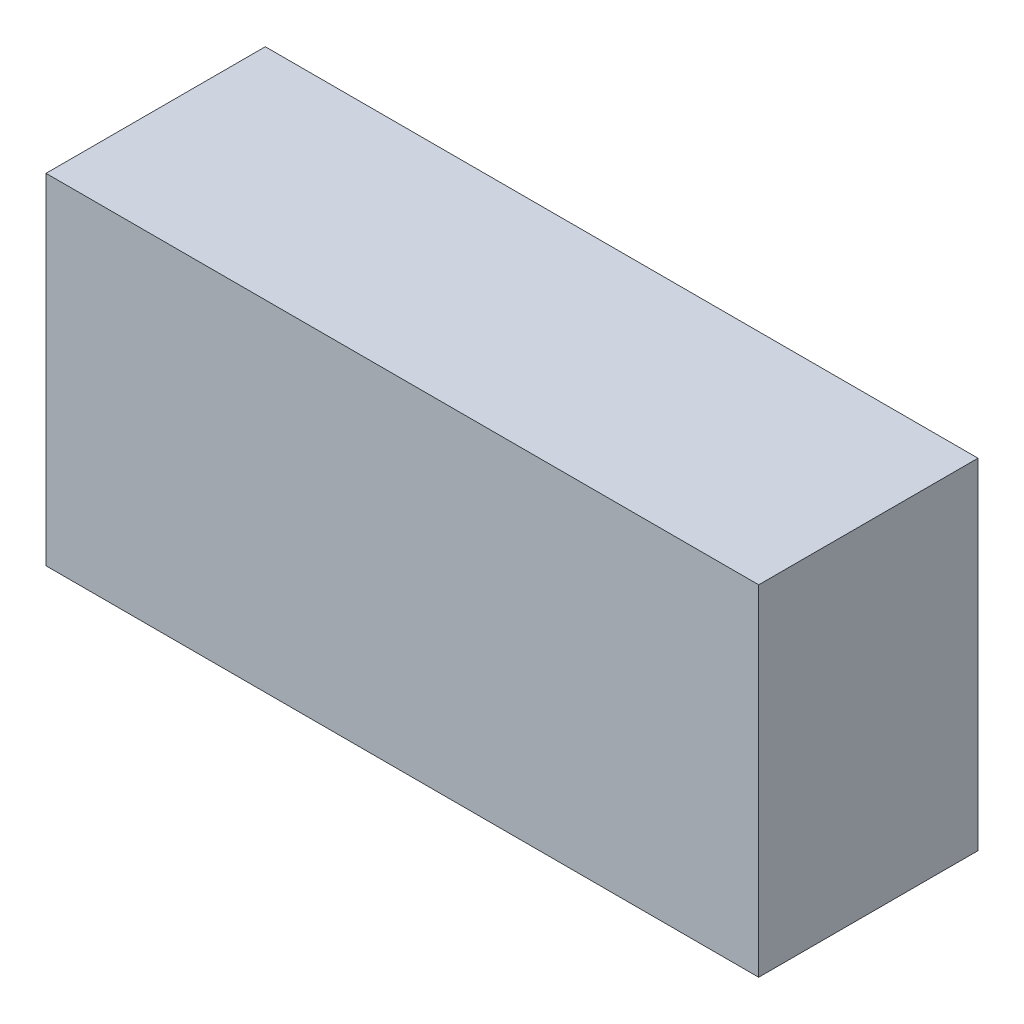
SolidWorks part; units mm, degrees
ref_plane "Спереди" through (0, 0, 0) normal (0, 0, 1) x (1, 0, 0)
ref_plane "Сверху" through (0, 0, 0) normal (0, 1, 0) x (1, 0, 0)
ref_plane "Справа" through (0, 0, 0) normal (1, 0, 0) x (0, 0, -1)
sketch "Эскиз1" plane through (0, 0, 0) normal (0, 1, 0) x (1, 0, 0)
  line L1 (-9.75, 3) -> (9.75, 3)
  line L2 (-9.75, 3) -> (-9.75, -3)
  line L3 (-9.75, -3) -> (9.75, -3)
  line L4 (9.75, 3) -> (9.75, -3)
  line L5 (-9.75, 3) -> (9.75, -3) construction
  line L6 (-9.75, -3) -> (9.75, 3) construction
  point P0 (0, 0)
  dimension "D1" = 19.5
  dimension "D2" = 6
extrude "Бобышка-Вытянуть1" add sketch "Эскиз1" along normal blind 9.3
sketch "Эскиз2" plane through (0, 0, 0) normal (0, -1, 0) x (1, 0, 0)
  line L0 (9.75, -3) -> (-9.75, -3) construction
  line L1 (-7.92, -1.2) -> (-7.32, -1.2)
  line L2 (-7.92, -1.2) -> (-7.92, -1.5)
  line L3 (-7.92, -1.5) -> (-7.32, -1.5)
  line L4 (-7.32, -1.2) -> (-7.32, -1.5)
  line L5 (-7.92, -1.2) -> (-7.32, -1.5) construction
  line L6 (-7.92, -1.5) -> (-7.32, -1.2) construction
  line L7 (-9.75, -3) -> (-9.75, 3) construction
  line L8 (-7.9208, -1.1995) -> (-7.3208, -1.1995)
  line L9 (-7.9208, -1.1995) -> (-7.9208, -1.4995)
  line L10 (-7.9208, -1.4995) -> (-7.3208, -1.4995)
  line L11 (-7.3208, -1.1995) -> (-7.3208, -1.4995)
  line L13 (-5.38, -1.2) -> (-4.78, -1.2)
  line L14 (-5.38, -1.2) -> (-5.38, -1.5)
  line L15 (-5.38, -1.5) -> (-4.78, -1.5)
  line L16 (-4.78, -1.2) -> (-4.78, -1.5)
  line L17 (-5.38, -1.2) -> (-4.78, -1.5) construction
  line L18 (-5.38, -1.5) -> (-4.78, -1.2) construction
  line L19 (-0.3, -1.2) -> (0.3, -1.2)
  line L20 (-0.3, -1.2) -> (-0.3, -1.5)
  line L21 (-0.3, -1.5) -> (0.3, -1.5)
  line L22 (0.3, -1.2) -> (0.3, -1.5)
  line L23 (-0.3, -1.2) -> (0.3, -1.5) construction
  line L24 (-0.3, -1.5) -> (0.3, -1.2) construction
  line L25 (2.24, -1.2) -> (2.84, -1.2)
  line L26 (2.24, -1.2) -> (2.24, -1.5)
  line L27 (2.24, -1.5) -> (2.84, -1.5)
  line L28 (2.84, -1.2) -> (2.84, -1.5)
  line L29 (2.24, -1.2) -> (2.84, -1.5) construction
  line L30 (2.24, -1.5) -> (2.84, -1.2) construction
  line L31 (4.78, -1.2) -> (5.38, -1.2)
  line L32 (4.78, -1.2) -> (4.78, -1.5)
  line L33 (4.78, -1.5) -> (5.38, -1.5)
  line L34 (5.38, -1.2) -> (5.38, -1.5)
  line L35 (4.78, -1.2) -> (5.38, -1.5) construction
  line L36 (4.78, -1.5) -> (5.38, -1.2) construction
  point P0 (-7.62, -1.35)
  point P9 (0, -1.35)
  point P17 (-5.08, -1.35)
  point P23 (2.54, -1.35)
  point P28 (5.08, -1.35)
  point P33 (0, 0)
  point P34 (0, 0)
  point P35 (2.54, -1.35)
  dimension "D1" = 1.65
  dimension "D2" = 2.13
  dimension "D3" = 0.6
  dimension "D4" = 0.3
  dimension "D5" = 0.6
  dimension "D6" = 0.6
  dimension "D7" = 0.6
  dimension "D8" = 0.6
  dimension "D9" = 0.3
  dimension "D10" = 0.3
  dimension "D11" = 0.3
  dimension "D12" = 0.3
  dimension "D13" = 1.65
  dimension "D14" = 1.65
  dimension "D15" = 1.65
  dimension "D16" = 1.65
  dimension "D17" = 2.54
  dimension "D18" = 5.08
  dimension "D19" = 2.54
  dimension "D20" = 2.54
extrude "Бобышка-Вытянуть2" add sketch "Эскиз2" along normal blind 3 contours L2 L3 L4 L1 | L14 L15 L16 L13 | L20 L21 L22 L19 | L26 L27 L28 L25 | L32 L33 L34 L31
sketch "Эскиз3" plane through (0, 9.3, 0) normal (0, 1, 0) x (1, 0, 0)
  text T0 "DC Converter" font "Century Gothic" height in points 10
extrude "Бобышка-Вытянуть3" add sketch "Эскиз3" against normal blind 0.2
